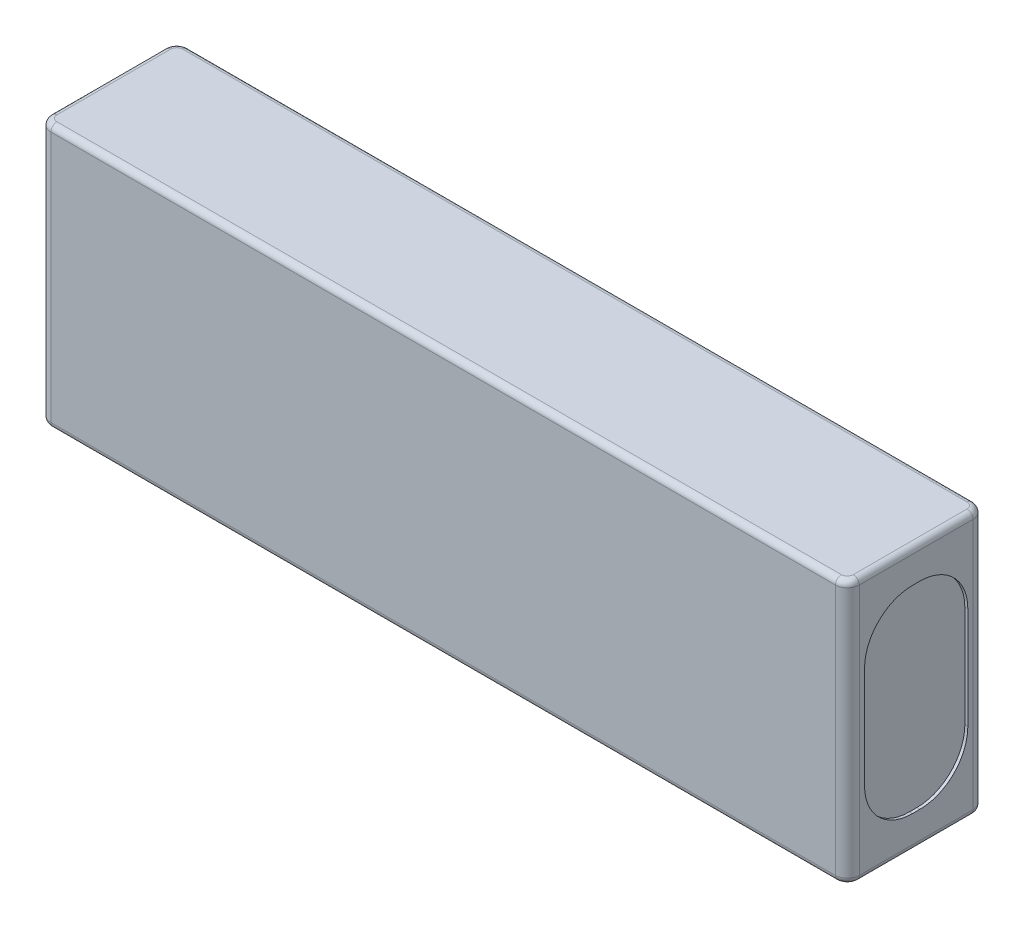
SolidWorks part; units mm, degrees
ref_plane "Front Plane" through (0, 0, 0) normal (0, 0, 1) x (1, 0, 0)
ref_plane "Top Plane" through (0, 0, 0) normal (0, 1, 0) x (1, 0, 0)
ref_plane "Right Plane" through (0, 0, 0) normal (1, 0, 0) x (0, 0, -1)
ref_plane "Plane1" through (0, 0, -15) normal (0, 0, -1) x (-1, 0, 0)
sketch "Sketch1" plane through (0, 0, -15) normal (0, 0, -1) x (-1, 0, 0)
  line L0 (-69, -22) -> (66, -22)
  line L1 (66, -22) -> (66, 22)
  line L2 (66, 22) -> (-69, 22)
  line L3 (-69, 22) -> (-69, -22)
  line L4 (-69, 0) -> (66, 0) construction
  line L5 (-1.5, 22) -> (-1.5, -22) construction
  dimension "D1" = 44
  dimension "D2" = 135
extrude "Boss-Extrude1" add sketch "Sketch1" against normal blind 23
sketch "Sketch2" plane through (69, 0, 0) normal (1, 0, 0) x (0, 0, -1)
  line L0 (-5.125, 8.5) -> (-5.125, -8.5)
  line L1 (2.875, -16.5) -> (4.125, -16.5)
  line L2 (12.125, -8.5) -> (12.125, 8.5)
  line L3 (4.125, 16.5) -> (2.875, 16.5)
  line L4 (-8, 22) -> (15, -22) construction
  line L5 (15, 22) -> (-8, -22) construction
  line L6 (-5.125, 16.5) -> (12.125, -16.5) construction
  line L7 (12.125, 16.5) -> (-5.125, -16.5) construction
  line L12 (-8, 22) -> (15, 22) construction
  line L13 (-8, 22) -> (-8, -22) construction
  line L14 (-8, -22) -> (15, -22) construction
  line L15 (15, 22) -> (15, -22) construction
  line L16 (-8, 22) -> (15, -22) construction
  line L17 (-8, -22) -> (15, 22) construction
  arc A0 (-5.125, -8.5) -> (2.875, -16.5) centre (2.875, -8.5) ccw
  arc A1 (4.125, -16.5) -> (12.125, -8.5) centre (4.125, -8.5) ccw
  arc A2 (12.125, 8.5) -> (4.125, 16.5) centre (4.125, 8.5) ccw
  arc A3 (-5.125, 8.5) -> (2.875, 16.5) centre (2.875, 8.5) cw
  point P16 (3.5, 0)
  dimension "D3" = 8
  dimension "D1" = 17.25
  dimension "D2" = 23
extrude "Cut-Extrude1" cut sketch "Sketch2" against normal blind 0.5
sketch "Sketch3" plane through (-66, 0, 0) normal (-1, 0, 0) x (0, 0, 1)
  line L0 (-2.875, 16.5) -> (-4.125, 16.5)
  line L1 (-12.125, 8.5) -> (-12.125, -8.5)
  line L2 (-4.125, -16.5) -> (-2.875, -16.5)
  line L3 (5.125, -8.5) -> (5.125, 8.5)
  line L4 (-12.125, 16.5) -> (5.125, -16.5) construction
  line L5 (5.125, 16.5) -> (-12.125, -16.5) construction
  line L6 (-15, 22) -> (8, -22) construction
  line L7 (8, -22) -> (-15, -22) construction
  line L8 (-15, -22) -> (8, 22) construction
  arc A0 (-12.125, -8.5) -> (-4.125, -16.5) centre (-4.125, -8.5) ccw
  arc A1 (-2.875, -16.5) -> (5.125, -8.5) centre (-2.875, -8.5) ccw
  arc A2 (-2.875, 16.5) -> (5.125, 8.5) centre (-2.875, 8.5) cw
  arc A3 (-4.125, 16.5) -> (-12.125, 8.5) centre (-4.125, 8.5) ccw
  dimension "D3" = 8
  dimension "D1" = 17.25
  dimension "D2" = 23
extrude "Cut-Extrude2" cut sketch "Sketch3" against normal blind 0.5
fillet "Fillet1" radius 2 4 edges at (-66, 0, -15) (-66, 0, 8) (69, 0, -15) (69, 0, 8)
fillet "Fillet2" radius 1 16 edges at (68.4142, 22, -14.4142) (69, 22, -3.5) (1.5, 22, -15) (68.4142, 22, 7.4142) (-65.4142, 22, -14.4142) (1.5, 22, 8) (-66, 22, -3.5) (-65.4142, 22, 7.4142) (-66, -22, -3.5) (-65.4142, -22, -14.4142) (-65.4142, -22, 7.4142) (1.5, -22, -15) (1.5, -22, 8) (68.4142, -22, -14.4142) (68.4142, -22, 7.4142) (69, -22, -3.5)
sketch "Sketch4" plane through (0, 0, 8) normal (0, 0, 1) x (1, 0, 0)
  line L0 (-64, 0) -> (67, 0) construction
  line L1 (-64, 21) -> (-64, -21) construction
  line L2 (67, -21) -> (67, 21) construction
  line L3 (1.5, 25.9735) -> (1.5, -21) construction
  line L4 (-64, -21) -> (67, -21) construction
  circle A0 centre (1.5, 0) radius 0.5026
equation "\"D1@Sketch3\"=\"D2@Sketch3\" * .75"
equation "\"D1@Sketch2\"=\"D2@Sketch2\"* .75"
